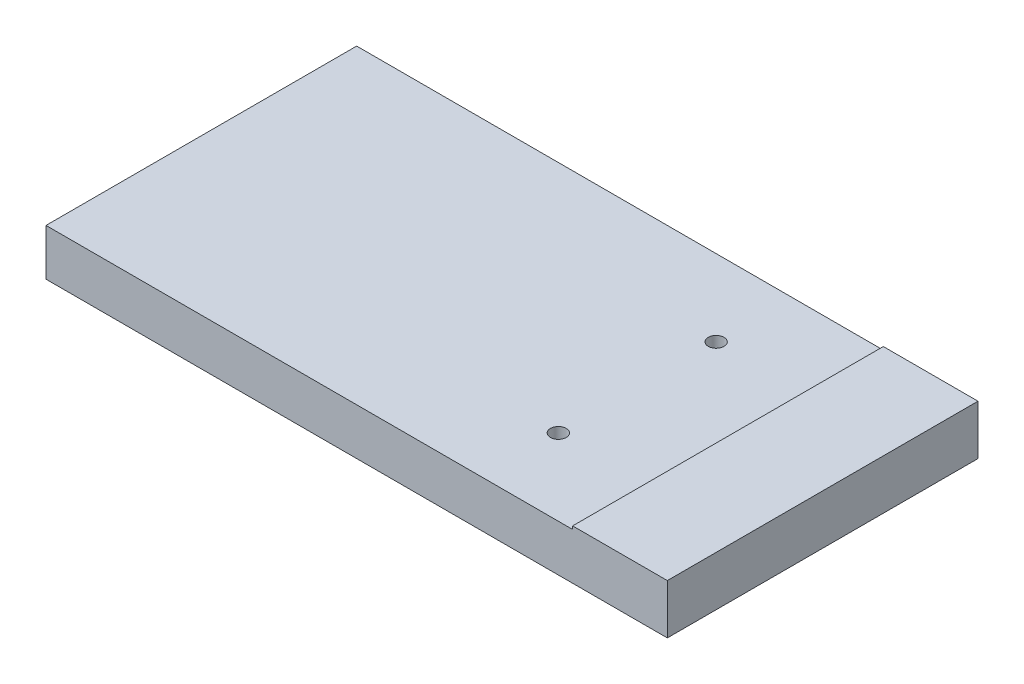
SolidWorks part; units mm, degrees
ref_plane "Front Plane" through (0, 0, 0) normal (0, 0, 1) x (1, 0, 0)
ref_plane "Top Plane" through (0, 0, 0) normal (0, 1, 0) x (1, 0, 0)
ref_plane "Right Plane" through (0, 0, 0) normal (1, 0, 0) x (0, 0, -1)
sketch "Sketch1" plane through (0, 0, 0) normal (0, 1, 0) x (1, 0, 0)
  line L1 (-1000, -500) -> (1000, -500)
  line L2 (-1000, -500) -> (-1000, 500)
  line L3 (-1000, 500) -> (1000, 500)
  line L4 (1000, -500) -> (1000, 500)
  line L5 (-1000, -500) -> (1000, 500) construction
  line L6 (-1000, 500) -> (1000, -500) construction
  point P0 (0, 0)
  dimension "D1" = 2000
  dimension "D2" = 1000
extrude "Boss-Extrude1" add sketch "Sketch1" along normal blind 150
sketch "Sketch2" plane through (0, 150, 0) normal (0, 1, 0) x (1, 0, 0)
  line L0 (-1000, -500) -> (1000, -500) construction
  line L1 (695.2, -500) -> (1000, -500)
  line L2 (695.2, -500) -> (695.2, 500)
  line L3 (695.2, 500) -> (1000, 500)
  line L4 (1000, -500) -> (1000, 500)
  line L5 (695.2, -500) -> (1000, 500) construction
  line L6 (695.2, 500) -> (1000, -500) construction
  point P0 (847.6, 0)
  point P5 (104.212, -298.45)
  dimension "D1" = 304.8
extrude "Boss-Extrude2" add sketch "Sketch2" along normal blind 10
sketch "Sketch3" plane through (0, 0, 0) normal (0, -1, 0) x (1, 0, 0)
  line L0 (0, 0) -> (318.0735, 0) construction
  line L1 (1000, 500) -> (1000, -500) construction
  circle A0 centre (403.1, 254) radius 25.4
  circle A1 centre (403.1, -254) radius 25.4
  dimension "D1" = 50.8
  dimension "D2" = 596.9
  dimension "D3" = 254
extrude "Cut-Extrude1" cut sketch "Sketch3" against normal through all
